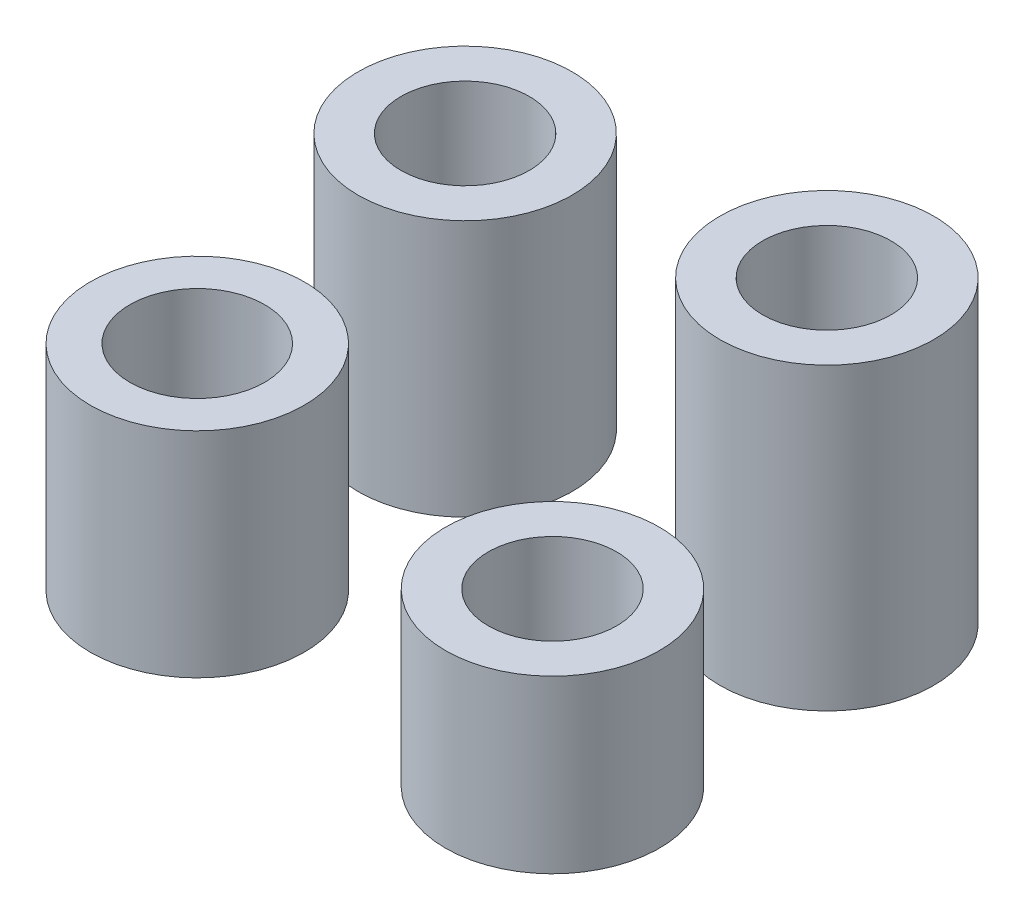
SolidWorks part; units mm, degrees
ref_plane "Front Plane" through (0, 0, 0) normal (0, 0, 1) x (1, 0, 0)
ref_plane "Top Plane" through (0, 0, 0) normal (0, 1, 0) x (1, 0, 0)
ref_plane "Right Plane" through (0, 0, 0) normal (1, 0, 0) x (0, 0, -1)
sketch "Sketch1" plane through (0, 0, 0) normal (0, 1, 0) x (1, 0, 0)
  circle A0 centre (-43.5694, 9.4173) radius 1.575
  circle A2 centre (-43.5694, 9.4173) radius 2.5
  dimension "D1" = 5
  dimension "D2" = 3.15
extrude "Boss-Extrude1" add sketch "Sketch1" along normal blind 5 contours A2 A0
sketch "Sketch2" plane through (0, 0, 0) normal (0, 1, 0) x (1, 0, 0)
  circle A0 centre (-35.4531, 9.6023) radius 1.5
  circle A1 centre (-35.4531, 9.6023) radius 2.5
  dimension "D1" = 3
  dimension "D2" = 5
extrude "Boss-Extrude2" add sketch "Sketch2" along normal blind 4 separate body
sketch "Sketch3" plane through (0, 0, 0) normal (0, 1, 0) x (1, 0, 0)
  circle A0 centre (-43.691, 15.7985) radius 1.5
  circle A1 centre (-43.691, 15.7985) radius 2.5
extrude "Boss-Extrude3" add sketch "Sketch3" along normal blind 6 separate body
sketch "Sketch4" plane through (0, 0, 0) normal (0, 1, 0) x (1, 0, 0)
  circle A0 centre (-35.542, 16.1029) radius 1.5
  circle A1 centre (-35.542, 16.1029) radius 2.5
  dimension "D1" = 3
  dimension "D2" = 5
extrude "Boss-Extrude4" add sketch "Sketch4" along normal blind 7 separate body
